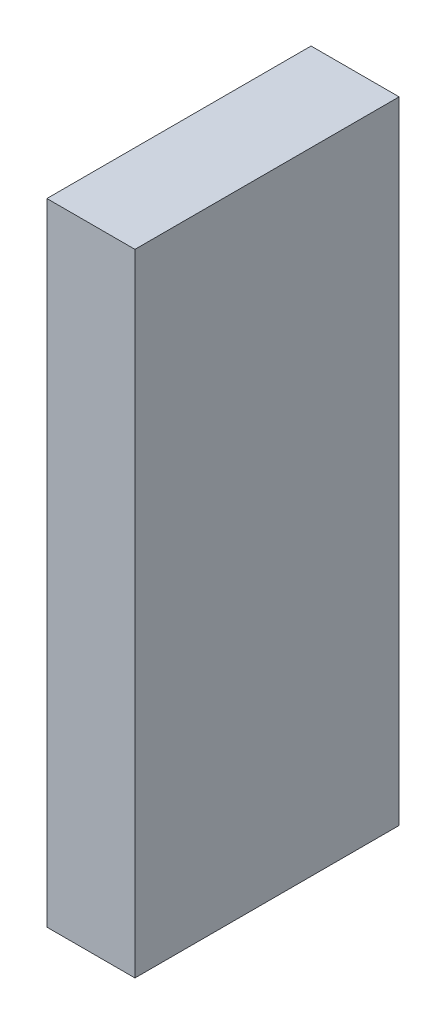
SolidWorks part; units mm, degrees
material "6063-T1"
ref_plane "Front Plane" through (0, 0, 0) normal (0, 0, 1) x (1, 0, 0)
ref_plane "Top Plane" through (0, 0, 0) normal (0, 1, 0) x (1, 0, 0)
ref_plane "Right Plane" through (0, 0, 0) normal (1, 0, 0) x (0, 0, -1)
sketch "Sketch1" plane through (0, 0, 0) normal (0, 1, 0) x (1, 0, 0)
  line L1 (-15, 45) -> (15, 45)
  line L2 (-15, 45) -> (-15, -45)
  line L3 (-15, -45) -> (15, -45)
  line L4 (15, 45) -> (15, -45)
  line L5 (-15, 45) -> (15, -45) construction
  line L6 (-15, -45) -> (15, 45) construction
  point P0 (0, 0)
  dimension "D1" = 30
  dimension "D2" = 90
extrude "Boss-Extrude1" add sketch "Sketch1" along normal mid plane 215
